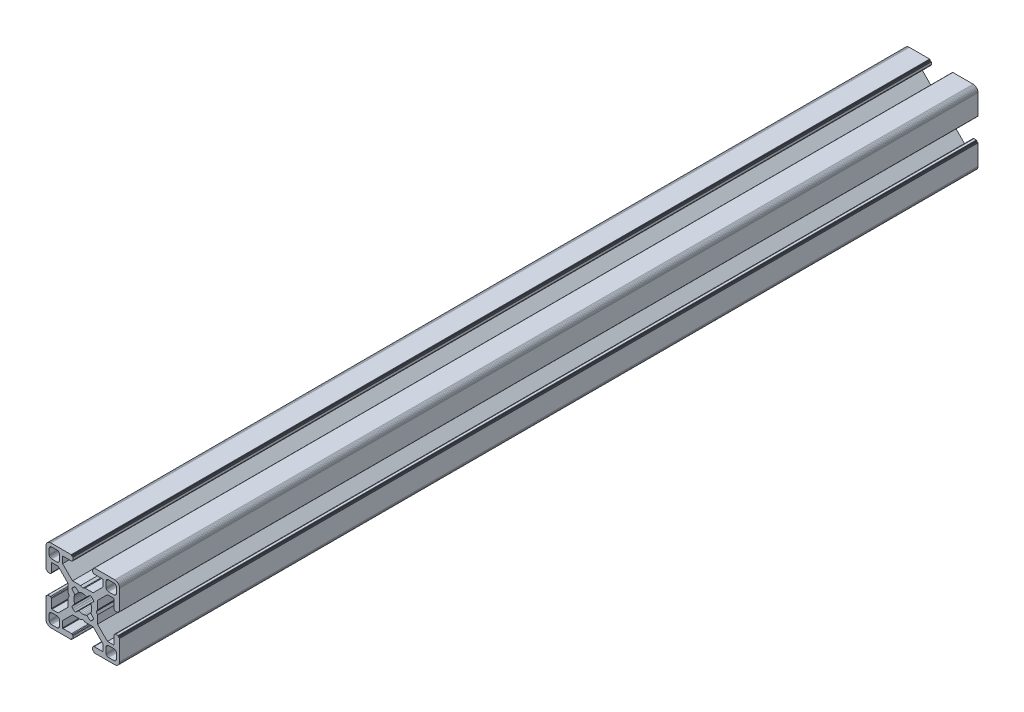
SolidWorks part; units mm, degrees
ref_plane "Front Plane" through (0, 0, 0) normal (0, 0, 1) x (1, 0, 0)
ref_plane "Top Plane" through (0, 0, 0) normal (0, 1, 0) x (1, 0, 0)
ref_plane "Right Plane" through (0, 0, 0) normal (1, 0, 0) x (0, 0, -1)
ref_plane "Plane1" through (0, 0, 0) normal (0, 0, 1) x (1, 0, 0)
sketch "Sketch1" plane through (0, 0, 0) normal (0, 0, 1) x (1, 0, 0)
  line L0 (28.3473, 29.9696) -> (28, 30)
  line L1 (28, 30) -> (19.75, 30)
  line L2 (19.75, 30) -> (19.7153, 29.997)
  line L3 (19.7153, 29.997) -> (19.6816, 29.9879)
  line L4 (19.6816, 29.9879) -> (19.65, 29.9732)
  line L5 (19.65, 29.9732) -> (19.6214, 29.9532)
  line L6 (19.6214, 29.9532) -> (19.5968, 29.9286)
  line L7 (19.5968, 29.9286) -> (19.5768, 29.9)
  line L8 (19.5768, 29.9) -> (19.5621, 29.8684)
  line L9 (19.5621, 29.8684) -> (19.553, 29.8347)
  line L10 (19.553, 29.8347) -> (19.55, 29.8)
  line L11 (19.55, 29.8) -> (19.55, 29.7)
  line L12 (19.55, 29.7) -> (19.547, 29.6653)
  line L13 (19.547, 29.6653) -> (19.5379, 29.6316)
  line L14 (19.5379, 29.6316) -> (19.5232, 29.6)
  line L15 (19.5232, 29.6) -> (19.5032, 29.5714)
  line L16 (19.5032, 29.5714) -> (19.4786, 29.5468)
  line L17 (19.4786, 29.5468) -> (19.45, 29.5268)
  line L18 (19.45, 29.5268) -> (19.4184, 29.5121)
  line L19 (19.4184, 29.5121) -> (19.3847, 29.503)
  line L20 (19.3847, 29.503) -> (19.35, 29.5)
  line L21 (19.35, 29.5) -> (19.25, 29.5)
  line L22 (19.25, 29.5) -> (19.2153, 29.497)
  line L23 (19.2153, 29.497) -> (19.1816, 29.4879)
  line L24 (19.1816, 29.4879) -> (19.15, 29.4732)
  line L25 (19.15, 29.4732) -> (19.1214, 29.4532)
  line L26 (19.1214, 29.4532) -> (19.0968, 29.4286)
  line L27 (19.0968, 29.4286) -> (19.0768, 29.4)
  line L28 (19.0768, 29.4) -> (19.0621, 29.3684)
  line L29 (19.0621, 29.3684) -> (19.053, 29.3347)
  line L30 (19.053, 29.3347) -> (19.05, 29.3)
  line L31 (19.05, 29.3) -> (19.05, 28.4)
  line L32 (19.05, 28.4) -> (19.0591, 28.2958)
  line L33 (19.0591, 28.2958) -> (19.0862, 28.1948)
  line L34 (19.0862, 28.1948) -> (19.1304, 28.1)
  line L35 (19.1304, 28.1) -> (19.1904, 28.0143)
  line L36 (19.1904, 28.0143) -> (19.2643, 27.9404)
  line L37 (19.2643, 27.9404) -> (19.35, 27.8804)
  line L38 (19.35, 27.8804) -> (19.4448, 27.8362)
  line L39 (19.4448, 27.8362) -> (19.5458, 27.8091)
  line L40 (19.5458, 27.8091) -> (19.65, 27.8)
  line L41 (19.65, 27.8) -> (23.05, 27.8)
  line L42 (23.05, 27.8) -> (23.0847, 27.7969)
  line L43 (23.0847, 27.7969) -> (23.1184, 27.7879)
  line L44 (23.1184, 27.7879) -> (23.15, 27.7732)
  line L45 (23.15, 27.7732) -> (23.1786, 27.7532)
  line L46 (23.1786, 27.7532) -> (23.2032, 27.7285)
  line L47 (23.2032, 27.7285) -> (23.2232, 27.7)
  line L48 (23.2232, 27.7) -> (23.2379, 27.6684)
  line L49 (23.2379, 27.6684) -> (23.247, 27.6347)
  line L50 (23.247, 27.6347) -> (23.25, 27.6)
  line L51 (23.25, 27.6) -> (23.25, 25.05)
  line L52 (23.25, 25.05) -> (19.2045, 21)
  line L53 (19.2045, 21) -> (15.9, 21)
  line L54 (15.9, 21) -> (15, 20.4848)
  line L55 (15, 20.4848) -> (14.1, 21)
  line L56 (14.1, 21) -> (10.7955, 21)
  line L57 (10.7955, 21) -> (7.9973, 23.8013)
  line L58 (7.9973, 23.8013) -> (6.75, 25.05)
  line L59 (6.75, 25.05) -> (6.75, 27.6)
  line L60 (6.75, 27.6) -> (6.753, 27.6347)
  line L61 (6.753, 27.6347) -> (6.7621, 27.6684)
  line L62 (6.7621, 27.6684) -> (6.7768, 27.7)
  line L63 (6.7768, 27.7) -> (6.7968, 27.7285)
  line L64 (6.7968, 27.7285) -> (6.8215, 27.7532)
  line L65 (6.8215, 27.7532) -> (6.85, 27.7732)
  line L66 (6.85, 27.7732) -> (6.8816, 27.7879)
  line L67 (6.8816, 27.7879) -> (6.9153, 27.7969)
  line L68 (6.9153, 27.7969) -> (6.95, 27.8)
  line L69 (6.95, 27.8) -> (10.35, 27.8)
  line L70 (10.35, 27.8) -> (10.4542, 27.8091)
  line L71 (10.4542, 27.8091) -> (10.5552, 27.8362)
  line L72 (10.5552, 27.8362) -> (10.65, 27.8804)
  line L73 (10.65, 27.8804) -> (10.7357, 27.9404)
  line L74 (10.7357, 27.9404) -> (10.8096, 28.0143)
  line L75 (10.8096, 28.0143) -> (10.8696, 28.1)
  line L76 (10.8696, 28.1) -> (10.9138, 28.1948)
  line L77 (10.9138, 28.1948) -> (10.9409, 28.2958)
  line L78 (10.9409, 28.2958) -> (10.95, 28.4)
  line L79 (10.95, 28.4) -> (10.95, 29.3)
  line L80 (10.95, 29.3) -> (10.947, 29.3347)
  line L81 (10.947, 29.3347) -> (10.938, 29.3684)
  line L82 (10.938, 29.3684) -> (10.9232, 29.4)
  line L83 (10.9232, 29.4) -> (10.9032, 29.4286)
  line L84 (10.9032, 29.4286) -> (10.8786, 29.4532)
  line L85 (10.8786, 29.4532) -> (10.85, 29.4732)
  line L86 (10.85, 29.4732) -> (10.8184, 29.4879)
  line L87 (10.8184, 29.4879) -> (10.7847, 29.497)
  line L88 (10.7847, 29.497) -> (10.75, 29.5)
  line L89 (10.75, 29.5) -> (10.65, 29.5)
  line L90 (10.65, 29.5) -> (10.6153, 29.503)
  line L91 (10.6153, 29.503) -> (10.5816, 29.5121)
  line L92 (10.5816, 29.5121) -> (10.55, 29.5268)
  line L93 (10.55, 29.5268) -> (10.5214, 29.5468)
  line L94 (10.5214, 29.5468) -> (10.4968, 29.5714)
  line L95 (10.4968, 29.5714) -> (10.4768, 29.6)
  line L96 (10.4768, 29.6) -> (10.4621, 29.6316)
  line L97 (10.4621, 29.6316) -> (10.453, 29.6653)
  line L98 (10.453, 29.6653) -> (10.45, 29.7)
  line L99 (10.45, 29.7) -> (10.45, 29.8)
  line L100 (10.45, 29.8) -> (10.447, 29.8347)
  line L101 (10.447, 29.8347) -> (10.4379, 29.8684)
  line L102 (10.4379, 29.8684) -> (10.4232, 29.9)
  line L103 (10.4232, 29.9) -> (10.4032, 29.9286)
  line L104 (10.4032, 29.9286) -> (10.3786, 29.9532)
  line L105 (10.3786, 29.9532) -> (10.35, 29.9732)
  line L106 (10.35, 29.9732) -> (10.3184, 29.9879)
  line L107 (10.3184, 29.9879) -> (10.2847, 29.997)
  line L108 (10.2847, 29.997) -> (10.25, 30)
  line L109 (10.25, 30) -> (2, 30)
  line L110 (2, 30) -> (1.6527, 29.9696)
  line L111 (1.6527, 29.9696) -> (1.316, 29.8794)
  line L112 (1.316, 29.8794) -> (1, 29.7321)
  line L113 (1, 29.7321) -> (0.7144, 29.5321)
  line L114 (0.7144, 29.5321) -> (0.4679, 29.2856)
  line L115 (0.4679, 29.2856) -> (0.2679, 29)
  line L116 (0.2679, 29) -> (0.1206, 28.684)
  line L117 (0.1206, 28.684) -> (0.0304, 28.3473)
  line L118 (0.0304, 28.3473) -> (0, 28)
  line L119 (0, 28) -> (0, 19.75)
  line L120 (0, 19.75) -> (0.003, 19.7153)
  line L121 (0.003, 19.7153) -> (0.0121, 19.6816)
  line L122 (0.0121, 19.6816) -> (0.0268, 19.65)
  line L123 (0.0268, 19.65) -> (0.0468, 19.6214)
  line L124 (0.0468, 19.6214) -> (0.0714, 19.5968)
  line L125 (0.0714, 19.5968) -> (0.1, 19.5768)
  line L126 (0.1, 19.5768) -> (0.1316, 19.5621)
  line L127 (0.1316, 19.5621) -> (0.1653, 19.553)
  line L128 (0.1653, 19.553) -> (0.2, 19.55)
  line L129 (0.2, 19.55) -> (0.3, 19.55)
  line L130 (0.3, 19.55) -> (0.3347, 19.547)
  line L131 (0.3347, 19.547) -> (0.3684, 19.5379)
  line L132 (0.3684, 19.5379) -> (0.4, 19.5232)
  line L133 (0.4, 19.5232) -> (0.4286, 19.5032)
  line L134 (0.4286, 19.5032) -> (0.4532, 19.4786)
  line L135 (0.4532, 19.4786) -> (0.4732, 19.45)
  line L136 (0.4732, 19.45) -> (0.4879, 19.4184)
  line L137 (0.4879, 19.4184) -> (0.497, 19.3847)
  line L138 (0.497, 19.3847) -> (0.5, 19.35)
  line L139 (0.5, 19.35) -> (0.5, 19.25)
  line L140 (0.5, 19.25) -> (0.503, 19.2153)
  line L141 (0.503, 19.2153) -> (0.5121, 19.1816)
  line L142 (0.5121, 19.1816) -> (0.5268, 19.15)
  line L143 (0.5268, 19.15) -> (0.5468, 19.1214)
  line L144 (0.5468, 19.1214) -> (0.5714, 19.0968)
  line L145 (0.5714, 19.0968) -> (0.6, 19.0768)
  line L146 (0.6, 19.0768) -> (0.6316, 19.0621)
  line L147 (0.6316, 19.0621) -> (0.6653, 19.053)
  line L148 (0.6653, 19.053) -> (0.7, 19.05)
  line L149 (0.7, 19.05) -> (1.6, 19.05)
  line L150 (1.6, 19.05) -> (1.7042, 19.0591)
  line L151 (1.7042, 19.0591) -> (1.8052, 19.0862)
  line L152 (1.8052, 19.0862) -> (1.9, 19.1304)
  line L153 (1.9, 19.1304) -> (1.9857, 19.1904)
  line L154 (1.9857, 19.1904) -> (2.0596, 19.2643)
  line L155 (2.0596, 19.2643) -> (2.1196, 19.35)
  line L156 (2.1196, 19.35) -> (2.1638, 19.4448)
  line L157 (2.1638, 19.4448) -> (2.1909, 19.5458)
  line L158 (2.1909, 19.5458) -> (2.2, 19.65)
  line L159 (2.2, 19.65) -> (2.2, 23.05)
  line L160 (2.2, 23.05) -> (2.203, 23.0847)
  line L161 (2.203, 23.0847) -> (2.2121, 23.1184)
  line L162 (2.2121, 23.1184) -> (2.2268, 23.15)
  line L163 (2.2268, 23.15) -> (2.2468, 23.1786)
  line L164 (2.2468, 23.1786) -> (2.2714, 23.2032)
  line L165 (2.2714, 23.2032) -> (2.3, 23.2232)
  line L166 (2.3, 23.2232) -> (2.3316, 23.2379)
  line L167 (2.3316, 23.2379) -> (2.3653, 23.247)
  line L168 (2.3653, 23.247) -> (2.4, 23.25)
  line L169 (2.4, 23.25) -> (4.95, 23.25)
  line L170 (4.95, 23.25) -> (7.9973, 20.2027)
  line L171 (7.9973, 20.2027) -> (8.9955, 19.2045)
  line L172 (8.9955, 19.2045) -> (8.9955, 15.9)
  line L173 (8.9955, 15.9) -> (9.5151, 15)
  line L174 (9.5151, 15) -> (8.9955, 14.1)
  line L175 (8.9955, 14.1) -> (8.9955, 10.7955)
  line L176 (8.9955, 10.7955) -> (4.95, 6.75)
  line L177 (4.95, 6.75) -> (2.4, 6.75)
  line L178 (2.4, 6.75) -> (2.3653, 6.753)
  line L179 (2.3653, 6.753) -> (2.3316, 6.7621)
  line L180 (2.3316, 6.7621) -> (2.3, 6.7768)
  line L181 (2.3, 6.7768) -> (2.2714, 6.7968)
  line L182 (2.2714, 6.7968) -> (2.2468, 6.8214)
  line L183 (2.2468, 6.8214) -> (2.2268, 6.85)
  line L184 (2.2268, 6.85) -> (2.2121, 6.8816)
  line L185 (2.2121, 6.8816) -> (2.203, 6.9153)
  line L186 (2.203, 6.9153) -> (2.2, 6.95)
  line L187 (2.2, 6.95) -> (2.2, 10.35)
  line L188 (2.2, 10.35) -> (2.1909, 10.4542)
  line L189 (2.1909, 10.4542) -> (2.1638, 10.5552)
  line L190 (2.1638, 10.5552) -> (2.1196, 10.65)
  line L191 (2.1196, 10.65) -> (2.0596, 10.7357)
  line L192 (2.0596, 10.7357) -> (1.9857, 10.8096)
  line L193 (1.9857, 10.8096) -> (1.9, 10.8696)
  line L194 (1.9, 10.8696) -> (1.8052, 10.9138)
  line L195 (1.8052, 10.9138) -> (1.7042, 10.9409)
  line L196 (1.7042, 10.9409) -> (1.6, 10.95)
  line L197 (1.6, 10.95) -> (0.7, 10.95)
  line L198 (0.7, 10.95) -> (0.6653, 10.9469)
  line L199 (0.6653, 10.9469) -> (0.6316, 10.9379)
  line L200 (0.6316, 10.9379) -> (0.6, 10.9232)
  line L201 (0.6, 10.9232) -> (0.5715, 10.9032)
  line L202 (0.5715, 10.9032) -> (0.5468, 10.8785)
  line L203 (0.5468, 10.8785) -> (0.5268, 10.85)
  line L204 (0.5268, 10.85) -> (0.5121, 10.8184)
  line L205 (0.5121, 10.8184) -> (0.503, 10.7847)
  line L206 (0.503, 10.7847) -> (0.5, 10.75)
  line L207 (0.5, 10.75) -> (0.5, 10.65)
  line L208 (0.5, 10.65) -> (0.497, 10.6153)
  line L209 (0.497, 10.6153) -> (0.4879, 10.5816)
  line L210 (0.4879, 10.5816) -> (0.4732, 10.55)
  line L211 (0.4732, 10.55) -> (0.4532, 10.5214)
  line L212 (0.4532, 10.5214) -> (0.4286, 10.4968)
  line L213 (0.4286, 10.4968) -> (0.4, 10.4768)
  line L214 (0.4, 10.4768) -> (0.3684, 10.4621)
  line L215 (0.3684, 10.4621) -> (0.3347, 10.453)
  line L216 (0.3347, 10.453) -> (0.3, 10.45)
  line L217 (0.3, 10.45) -> (0.2, 10.45)
  line L218 (0.2, 10.45) -> (0.1653, 10.447)
  line L219 (0.1653, 10.447) -> (0.1316, 10.4379)
  line L220 (0.1316, 10.4379) -> (0.1, 10.4232)
  line L221 (0.1, 10.4232) -> (0.0714, 10.4032)
  line L222 (0.0714, 10.4032) -> (0.0468, 10.3786)
  line L223 (0.0468, 10.3786) -> (0.0268, 10.35)
  line L224 (0.0268, 10.35) -> (0.0121, 10.3184)
  line L225 (0.0121, 10.3184) -> (0.003, 10.2847)
  line L226 (0.003, 10.2847) -> (0, 10.25)
  line L227 (0, 10.25) -> (0, 2)
  line L228 (0, 2) -> (0.0304, 1.6527)
  line L229 (0.0304, 1.6527) -> (0.1206, 1.316)
  line L230 (0.1206, 1.316) -> (0.2679, 1)
  line L231 (0.2679, 1) -> (0.4679, 0.7144)
  line L232 (0.4679, 0.7144) -> (0.7144, 0.4679)
  line L233 (0.7144, 0.4679) -> (1, 0.2679)
  line L234 (1, 0.2679) -> (1.316, 0.1206)
  line L235 (1.316, 0.1206) -> (1.6527, 0.0304)
  line L236 (1.6527, 0.0304) -> (2, 0)
  line L237 (2, 0) -> (10.25, 0)
  line L238 (10.25, 0) -> (10.2847, 0.003)
  line L239 (10.2847, 0.003) -> (10.3184, 0.0121)
  line L240 (10.3184, 0.0121) -> (10.35, 0.0268)
  line L241 (10.35, 0.0268) -> (10.3786, 0.0468)
  line L242 (10.3786, 0.0468) -> (10.4032, 0.0714)
  line L243 (10.4032, 0.0714) -> (10.4232, 0.1)
  line L244 (10.4232, 0.1) -> (10.4379, 0.1316)
  line L245 (10.4379, 0.1316) -> (10.447, 0.1653)
  line L246 (10.447, 0.1653) -> (10.45, 0.2)
  line L247 (10.45, 0.2) -> (10.45, 0.3)
  line L248 (10.45, 0.3) -> (10.453, 0.3347)
  line L249 (10.453, 0.3347) -> (10.4621, 0.3684)
  line L250 (10.4621, 0.3684) -> (10.4768, 0.4)
  line L251 (10.4768, 0.4) -> (10.4968, 0.4286)
  line L252 (10.4968, 0.4286) -> (10.5214, 0.4532)
  line L253 (10.5214, 0.4532) -> (10.55, 0.4732)
  line L254 (10.55, 0.4732) -> (10.5816, 0.4879)
  line L255 (10.5816, 0.4879) -> (10.6153, 0.497)
  line L256 (10.6153, 0.497) -> (10.65, 0.5)
  line L257 (10.65, 0.5) -> (10.75, 0.5)
  line L258 (10.75, 0.5) -> (10.7847, 0.503)
  line L259 (10.7847, 0.503) -> (10.8184, 0.5121)
  line L260 (10.8184, 0.5121) -> (10.85, 0.5268)
  line L261 (10.85, 0.5268) -> (10.8785, 0.5468)
  line L262 (10.8785, 0.5468) -> (10.9032, 0.5715)
  line L263 (10.9032, 0.5715) -> (10.9232, 0.6)
  line L264 (10.9232, 0.6) -> (10.9379, 0.6316)
  line L265 (10.9379, 0.6316) -> (10.9469, 0.6653)
  line L266 (10.9469, 0.6653) -> (10.95, 0.7)
  line L267 (10.95, 0.7) -> (10.95, 1.6)
  line L268 (10.95, 1.6) -> (10.9409, 1.7042)
  line L269 (10.9409, 1.7042) -> (10.9138, 1.8052)
  line L270 (10.9138, 1.8052) -> (10.8696, 1.9)
  line L271 (10.8696, 1.9) -> (10.8096, 1.9857)
  line L272 (10.8096, 1.9857) -> (10.7357, 2.0596)
  line L273 (10.7357, 2.0596) -> (10.65, 2.1196)
  line L274 (10.65, 2.1196) -> (10.5552, 2.1638)
  line L275 (10.5552, 2.1638) -> (10.4542, 2.1909)
  line L276 (10.4542, 2.1909) -> (10.35, 2.2)
  line L277 (10.35, 2.2) -> (6.95, 2.2)
  line L278 (6.95, 2.2) -> (6.9153, 2.203)
  line L279 (6.9153, 2.203) -> (6.8816, 2.212)
  line L280 (6.8816, 2.212) -> (6.85, 2.2268)
  line L281 (6.85, 2.2268) -> (6.8215, 2.2468)
  line L282 (6.8215, 2.2468) -> (6.7968, 2.2714)
  line L283 (6.7968, 2.2714) -> (6.7768, 2.3)
  line L284 (6.7768, 2.3) -> (6.7621, 2.3316)
  line L285 (6.7621, 2.3316) -> (6.753, 2.3653)
  line L286 (6.753, 2.3653) -> (6.75, 2.4)
  line L287 (6.75, 2.4) -> (6.75, 4.95)
  line L288 (6.75, 4.95) -> (9.7875, 7.9908)
  line L289 (9.7875, 7.9908) -> (10.7955, 9)
  line L290 (10.7955, 9) -> (14.1, 9)
  line L291 (14.1, 9) -> (15, 9.5151)
  line L292 (15, 9.5151) -> (15.9, 9)
  line L293 (15.9, 9) -> (19.2045, 9)
  line L294 (19.2045, 9) -> (20.2126, 7.9908)
  line L295 (20.2126, 7.9908) -> (23.25, 4.95)
  line L296 (23.25, 4.95) -> (23.25, 2.4)
  line L297 (23.25, 2.4) -> (23.247, 2.3653)
  line L298 (23.247, 2.3653) -> (23.2379, 2.3316)
  line L299 (23.2379, 2.3316) -> (23.2232, 2.3)
  line L300 (23.2232, 2.3) -> (23.2032, 2.2714)
  line L301 (23.2032, 2.2714) -> (23.1786, 2.2468)
  line L302 (23.1786, 2.2468) -> (23.15, 2.2268)
  line L303 (23.15, 2.2268) -> (23.1184, 2.212)
  line L304 (23.1184, 2.212) -> (23.0847, 2.203)
  line L305 (23.0847, 2.203) -> (23.05, 2.2)
  line L306 (23.05, 2.2) -> (19.65, 2.2)
  line L307 (19.65, 2.2) -> (19.5458, 2.1909)
  line L308 (19.5458, 2.1909) -> (19.4448, 2.1638)
  line L309 (19.4448, 2.1638) -> (19.35, 2.1196)
  line L310 (19.35, 2.1196) -> (19.2643, 2.0596)
  line L311 (19.2643, 2.0596) -> (19.1904, 1.9857)
  line L312 (19.1904, 1.9857) -> (19.1304, 1.9)
  line L313 (19.1304, 1.9) -> (19.0862, 1.8052)
  line L314 (19.0862, 1.8052) -> (19.0591, 1.7042)
  line L315 (19.0591, 1.7042) -> (19.05, 1.6)
  line L316 (19.05, 1.6) -> (19.05, 0.7)
  line L317 (19.05, 0.7) -> (19.053, 0.6653)
  line L318 (19.053, 0.6653) -> (19.0621, 0.6316)
  line L319 (19.0621, 0.6316) -> (19.0768, 0.6)
  line L320 (19.0768, 0.6) -> (19.0968, 0.5714)
  line L321 (19.0968, 0.5714) -> (19.1214, 0.5468)
  line L322 (19.1214, 0.5468) -> (19.15, 0.5268)
  line L323 (19.15, 0.5268) -> (19.1816, 0.5121)
  line L324 (19.1816, 0.5121) -> (19.2153, 0.503)
  line L325 (19.2153, 0.503) -> (19.25, 0.5)
  line L326 (19.25, 0.5) -> (19.35, 0.5)
  line L327 (19.35, 0.5) -> (19.3847, 0.497)
  line L328 (19.3847, 0.497) -> (19.4184, 0.4879)
  line L329 (19.4184, 0.4879) -> (19.45, 0.4732)
  line L330 (19.45, 0.4732) -> (19.4786, 0.4532)
  line L331 (19.4786, 0.4532) -> (19.5032, 0.4286)
  line L332 (19.5032, 0.4286) -> (19.5232, 0.4)
  line L333 (19.5232, 0.4) -> (19.5379, 0.3684)
  line L334 (19.5379, 0.3684) -> (19.547, 0.3347)
  line L335 (19.547, 0.3347) -> (19.55, 0.3)
  line L336 (19.55, 0.3) -> (19.55, 0.2)
  line L337 (19.55, 0.2) -> (19.553, 0.1653)
  line L338 (19.553, 0.1653) -> (19.5621, 0.1316)
  line L339 (19.5621, 0.1316) -> (19.5768, 0.1)
  line L340 (19.5768, 0.1) -> (19.5968, 0.0714)
  line L341 (19.5968, 0.0714) -> (19.6214, 0.0468)
  line L342 (19.6214, 0.0468) -> (19.65, 0.0268)
  line L343 (19.65, 0.0268) -> (19.6816, 0.0121)
  line L344 (19.6816, 0.0121) -> (19.7153, 0.003)
  line L345 (19.7153, 0.003) -> (19.75, 0)
  line L346 (19.75, 0) -> (28, 0)
  line L347 (28, 0) -> (28.3473, 0.0304)
  line L348 (28.3473, 0.0304) -> (28.684, 0.1206)
  line L349 (28.684, 0.1206) -> (29, 0.2679)
  line L350 (29, 0.2679) -> (29.2856, 0.4679)
  line L351 (29.2856, 0.4679) -> (29.5321, 0.7144)
  line L352 (29.5321, 0.7144) -> (29.7321, 1)
  line L353 (29.7321, 1) -> (29.8794, 1.316)
  line L354 (29.8794, 1.316) -> (29.9696, 1.6527)
  line L355 (29.9696, 1.6527) -> (30, 2)
  line L356 (30, 2) -> (30, 10.25)
  line L357 (30, 10.25) -> (29.997, 10.2847)
  line L358 (29.997, 10.2847) -> (29.988, 10.3184)
  line L359 (29.988, 10.3184) -> (29.9732, 10.35)
  line L360 (29.9732, 10.35) -> (29.9532, 10.3785)
  line L361 (29.9532, 10.3785) -> (29.9286, 10.4032)
  line L362 (29.9286, 10.4032) -> (29.9, 10.4232)
  line L363 (29.9, 10.4232) -> (29.8684, 10.4379)
  line L364 (29.8684, 10.4379) -> (29.8347, 10.447)
  line L365 (29.8347, 10.447) -> (29.8, 10.45)
  line L366 (29.8, 10.45) -> (29.7, 10.45)
  line L367 (29.7, 10.45) -> (29.6649, 10.4534)
  line L368 (29.6649, 10.4534) -> (29.6312, 10.4624)
  line L369 (29.6312, 10.4624) -> (29.5996, 10.4772)
  line L370 (29.5996, 10.4772) -> (29.5711, 10.4972)
  line L371 (29.5711, 10.4972) -> (29.5464, 10.5218)
  line L372 (29.5464, 10.5218) -> (29.5264, 10.5504)
  line L373 (29.5264, 10.5504) -> (29.5117, 10.582)
  line L374 (29.5117, 10.582) -> (29.5027, 10.6156)
  line L375 (29.5027, 10.6156) -> (29.4996, 10.6504)
  line L376 (29.4996, 10.6504) -> (29.4996, 10.7504)
  line L377 (29.4996, 10.7504) -> (29.497, 10.7847)
  line L378 (29.497, 10.7847) -> (29.4879, 10.8184)
  line L379 (29.4879, 10.8184) -> (29.4732, 10.85)
  line L380 (29.4732, 10.85) -> (29.4532, 10.8785)
  line L381 (29.4532, 10.8785) -> (29.4286, 10.9032)
  line L382 (29.4286, 10.9032) -> (29.4, 10.9232)
  line L383 (29.4, 10.9232) -> (29.3684, 10.9379)
  line L384 (29.3684, 10.9379) -> (29.3347, 10.9469)
  line L385 (29.3347, 10.9469) -> (29.3, 10.95)
  line L386 (29.3, 10.95) -> (28.4, 10.95)
  line L387 (28.4, 10.95) -> (28.2958, 10.9409)
  line L388 (28.2958, 10.9409) -> (28.1948, 10.9138)
  line L389 (28.1948, 10.9138) -> (28.1, 10.8696)
  line L390 (28.1, 10.8696) -> (28.0143, 10.8096)
  line L391 (28.0143, 10.8096) -> (27.9404, 10.7357)
  line L392 (27.9404, 10.7357) -> (27.8804, 10.65)
  line L393 (27.8804, 10.65) -> (27.8362, 10.5552)
  line L394 (27.8362, 10.5552) -> (27.8091, 10.4542)
  line L395 (27.8091, 10.4542) -> (27.8, 10.35)
  line L396 (27.8, 10.35) -> (27.8, 6.95)
  line L397 (27.8, 6.95) -> (27.797, 6.9153)
  line L398 (27.797, 6.9153) -> (27.7879, 6.8816)
  line L399 (27.7879, 6.8816) -> (27.7732, 6.85)
  line L400 (27.7732, 6.85) -> (27.7532, 6.8214)
  line L401 (27.7532, 6.8214) -> (27.7286, 6.7968)
  line L402 (27.7286, 6.7968) -> (27.7, 6.7768)
  line L403 (27.7, 6.7768) -> (27.6684, 6.7621)
  line L404 (27.6684, 6.7621) -> (27.6347, 6.753)
  line L405 (27.6347, 6.753) -> (27.6, 6.75)
  line L406 (27.6, 6.75) -> (25.05, 6.75)
  line L407 (25.05, 6.75) -> (23.8092, 7.9908)
  line L408 (23.8092, 7.9908) -> (21.0045, 10.7955)
  line L409 (21.0045, 10.7955) -> (21.0045, 14.1)
  line L410 (21.0045, 14.1) -> (20.4849, 15)
  line L411 (20.4849, 15) -> (21.0045, 15.9)
  line L412 (21.0045, 15.9) -> (21.0045, 19.2045)
  line L413 (21.0045, 19.2045) -> (25.05, 23.25)
  line L414 (25.05, 23.25) -> (27.6, 23.25)
  line L415 (27.6, 23.25) -> (27.6347, 23.247)
  line L416 (27.6347, 23.247) -> (27.6684, 23.2379)
  line L417 (27.6684, 23.2379) -> (27.7, 23.2232)
  line L418 (27.7, 23.2232) -> (27.7286, 23.2032)
  line L419 (27.7286, 23.2032) -> (27.7532, 23.1786)
  line L420 (27.7532, 23.1786) -> (27.7732, 23.15)
  line L421 (27.7732, 23.15) -> (27.7879, 23.1184)
  line L422 (27.7879, 23.1184) -> (27.797, 23.0847)
  line L423 (27.797, 23.0847) -> (27.8, 23.05)
  line L424 (27.8, 23.05) -> (27.8, 19.65)
  line L425 (27.8, 19.65) -> (27.8091, 19.5458)
  line L426 (27.8091, 19.5458) -> (27.8362, 19.4448)
  line L427 (27.8362, 19.4448) -> (27.8804, 19.35)
  line L428 (27.8804, 19.35) -> (27.9404, 19.2643)
  line L429 (27.9404, 19.2643) -> (28.0143, 19.1904)
  line L430 (28.0143, 19.1904) -> (28.1, 19.1304)
  line L431 (28.1, 19.1304) -> (28.1948, 19.0862)
  line L432 (28.1948, 19.0862) -> (28.2958, 19.0591)
  line L433 (28.2958, 19.0591) -> (28.4, 19.05)
  line L434 (28.4, 19.05) -> (29.3, 19.05)
  line L435 (29.3, 19.05) -> (29.3347, 19.053)
  line L436 (29.3347, 19.053) -> (29.3684, 19.0621)
  line L437 (29.3684, 19.0621) -> (29.4, 19.0768)
  line L438 (29.4, 19.0768) -> (29.4282, 19.0971)
  line L439 (29.4282, 19.0971) -> (29.4528, 19.1218)
  line L440 (29.4528, 19.1218) -> (29.4728, 19.1504)
  line L441 (29.4728, 19.1504) -> (29.4876, 19.182)
  line L442 (29.4876, 19.182) -> (29.4966, 19.2156)
  line L443 (29.4966, 19.2156) -> (29.4996, 19.2504)
  line L444 (29.4996, 19.2504) -> (29.4996, 19.3504)
  line L445 (29.4996, 19.3504) -> (29.5027, 19.3851)
  line L446 (29.5027, 19.3851) -> (29.5117, 19.4188)
  line L447 (29.5117, 19.4188) -> (29.5264, 19.4504)
  line L448 (29.5264, 19.4504) -> (29.5464, 19.4789)
  line L449 (29.5464, 19.4789) -> (29.5711, 19.5036)
  line L450 (29.5711, 19.5036) -> (29.5996, 19.5236)
  line L451 (29.5996, 19.5236) -> (29.6312, 19.5383)
  line L452 (29.6312, 19.5383) -> (29.6649, 19.5473)
  line L453 (29.6649, 19.5473) -> (29.7, 19.55)
  line L454 (29.7, 19.55) -> (29.8, 19.55)
  line L455 (29.8, 19.55) -> (29.8347, 19.553)
  line L456 (29.8347, 19.553) -> (29.8684, 19.5621)
  line L457 (29.8684, 19.5621) -> (29.9, 19.5768)
  line L458 (29.9, 19.5768) -> (29.9286, 19.5968)
  line L459 (29.9286, 19.5968) -> (29.9532, 19.6214)
  line L460 (29.9532, 19.6214) -> (29.9732, 19.65)
  line L461 (29.9732, 19.65) -> (29.9879, 19.6816)
  line L462 (29.9879, 19.6816) -> (29.997, 19.7153)
  line L463 (29.997, 19.7153) -> (30, 19.75)
  line L464 (30, 19.75) -> (30, 28)
  line L465 (30, 28) -> (29.9696, 28.3473)
  line L466 (29.9696, 28.3473) -> (29.8794, 28.684)
  line L467 (29.8794, 28.684) -> (29.7321, 29)
  line L468 (29.7321, 29) -> (29.5321, 29.2856)
  line L469 (29.5321, 29.2856) -> (29.2856, 29.5321)
  line L470 (29.2856, 29.5321) -> (29, 29.7321)
  line L471 (29, 29.7321) -> (28.684, 29.8794)
  line L472 (28.684, 29.8794) -> (28.3473, 29.9696)
  line L473 (1.3, 25.5) -> (1.3, 27.7)
  line L474 (1.3, 27.7) -> (1.3123, 27.8564)
  line L475 (1.3123, 27.8564) -> (1.3489, 28.009)
  line L476 (1.3489, 28.009) -> (1.409, 28.154)
  line L477 (1.409, 28.154) -> (1.491, 28.2878)
  line L478 (1.491, 28.2878) -> (1.5929, 28.4071)
  line L479 (1.5929, 28.4071) -> (1.7122, 28.509)
  line L480 (1.7122, 28.509) -> (1.846, 28.591)
  line L481 (1.846, 28.591) -> (1.991, 28.6511)
  line L482 (1.991, 28.6511) -> (2.1436, 28.6877)
  line L483 (2.1436, 28.6877) -> (2.3, 28.7)
  line L484 (2.3, 28.7) -> (4.5, 28.7)
  line L485 (4.5, 28.7) -> (4.6564, 28.6877)
  line L486 (4.6564, 28.6877) -> (4.809, 28.6511)
  line L487 (4.809, 28.6511) -> (4.954, 28.591)
  line L488 (4.954, 28.591) -> (5.0878, 28.509)
  line L489 (5.0878, 28.509) -> (5.2071, 28.4071)
  line L490 (5.2071, 28.4071) -> (5.309, 28.2878)
  line L491 (5.309, 28.2878) -> (5.391, 28.154)
  line L492 (5.391, 28.154) -> (5.4511, 28.009)
  line L493 (5.4511, 28.009) -> (5.4877, 27.8564)
  line L494 (5.4877, 27.8564) -> (5.5, 27.7)
  line L495 (5.5, 27.7) -> (5.5, 25.5)
  line L496 (5.5, 25.5) -> (5.4877, 25.3436)
  line L497 (5.4877, 25.3436) -> (5.4511, 25.191)
  line L498 (5.4511, 25.191) -> (5.391, 25.046)
  line L499 (5.391, 25.046) -> (5.309, 24.9122)
  line L500 (5.309, 24.9122) -> (5.2071, 24.7929)
  line L501 (5.2071, 24.7929) -> (5.0878, 24.691)
  line L502 (5.0878, 24.691) -> (4.954, 24.609)
  line L503 (4.954, 24.609) -> (4.809, 24.5489)
  line L504 (4.809, 24.5489) -> (4.6564, 24.5123)
  line L505 (4.6564, 24.5123) -> (4.5, 24.5)
  line L506 (4.5, 24.5) -> (2.3, 24.5)
  line L507 (2.3, 24.5) -> (2.1436, 24.5123)
  line L508 (2.1436, 24.5123) -> (1.991, 24.5489)
  line L509 (1.991, 24.5489) -> (1.846, 24.609)
  line L510 (1.846, 24.609) -> (1.7122, 24.691)
  line L511 (1.7122, 24.691) -> (1.5929, 24.7929)
  line L512 (1.5929, 24.7929) -> (1.491, 24.9122)
  line L513 (1.491, 24.9122) -> (1.409, 25.046)
  line L514 (1.409, 25.046) -> (1.3489, 25.191)
  line L515 (1.3489, 25.191) -> (1.3123, 25.3436)
  line L516 (1.3123, 25.3436) -> (1.3, 25.5)
  line L517 (25.3436, 28.6877) -> (25.5, 28.7)
  line L518 (25.5, 28.7) -> (27.7, 28.7)
  line L519 (27.7, 28.7) -> (27.8564, 28.6877)
  line L520 (27.8564, 28.6877) -> (28.009, 28.6511)
  line L521 (28.009, 28.6511) -> (28.154, 28.591)
  line L522 (28.154, 28.591) -> (28.2878, 28.509)
  line L523 (28.2878, 28.509) -> (28.4071, 28.4071)
  line L524 (28.4071, 28.4071) -> (28.509, 28.2878)
  line L525 (28.509, 28.2878) -> (28.591, 28.154)
  line L526 (28.591, 28.154) -> (28.6511, 28.009)
  line L527 (28.6511, 28.009) -> (28.6877, 27.8564)
  line L528 (28.6877, 27.8564) -> (28.7, 27.7)
  line L529 (28.7, 27.7) -> (28.7, 25.5)
  line L530 (28.7, 25.5) -> (28.6877, 25.3436)
  line L531 (28.6877, 25.3436) -> (28.6511, 25.191)
  line L532 (28.6511, 25.191) -> (28.591, 25.046)
  line L533 (28.591, 25.046) -> (28.509, 24.9122)
  line L534 (28.509, 24.9122) -> (28.4071, 24.7929)
  line L535 (28.4071, 24.7929) -> (28.2878, 24.691)
  line L536 (28.2878, 24.691) -> (28.154, 24.609)
  line L537 (28.154, 24.609) -> (28.009, 24.5489)
  line L538 (28.009, 24.5489) -> (27.8564, 24.5123)
  line L539 (27.8564, 24.5123) -> (27.7, 24.5)
  line L540 (27.7, 24.5) -> (25.5, 24.5)
  line L541 (25.5, 24.5) -> (25.3436, 24.5123)
  line L542 (25.3436, 24.5123) -> (25.191, 24.5489)
  line L543 (25.191, 24.5489) -> (25.046, 24.609)
  line L544 (25.046, 24.609) -> (24.9122, 24.691)
  line L545 (24.9122, 24.691) -> (24.7929, 24.7929)
  line L546 (24.7929, 24.7929) -> (24.691, 24.9122)
  line L547 (24.691, 24.9122) -> (24.609, 25.046)
  line L548 (24.609, 25.046) -> (24.5489, 25.191)
  line L549 (24.5489, 25.191) -> (24.5123, 25.3436)
  line L550 (24.5123, 25.3436) -> (24.5, 25.5)
  line L551 (24.5, 25.5) -> (24.5, 27.7)
  line L552 (24.5, 27.7) -> (24.5123, 27.8564)
  line L553 (24.5123, 27.8564) -> (24.5489, 28.009)
  line L554 (24.5489, 28.009) -> (24.609, 28.154)
  line L555 (24.609, 28.154) -> (24.691, 28.2878)
  line L556 (24.691, 28.2878) -> (24.7929, 28.4071)
  line L557 (24.7929, 28.4071) -> (24.9122, 28.509)
  line L558 (24.9122, 28.509) -> (25.046, 28.591)
  line L559 (25.046, 28.591) -> (25.191, 28.6511)
  line L560 (25.191, 28.6511) -> (25.3436, 28.6877)
  line L561 (15, 18.65) -> (15.55, 18.6083)
  line L562 (15.55, 18.6083) -> (16.0875, 18.4842)
  line L563 (16.0875, 18.4842) -> (16.6001, 18.2806)
  line L564 (16.6001, 18.2806) -> (18.1359, 19.5184)
  line L565 (18.1359, 19.5184) -> (18.645, 19.1187)
  line L566 (18.645, 19.1187) -> (19.1036, 18.6621)
  line L567 (19.1036, 18.6621) -> (19.5053, 18.1547)
  line L568 (19.5053, 18.1547) -> (18.2806, 16.6001)
  line L569 (18.2806, 16.6001) -> (18.4842, 16.0875)
  line L570 (18.4842, 16.0875) -> (18.6083, 15.55)
  line L571 (18.6083, 15.55) -> (18.65, 15)
  line L572 (18.65, 15) -> (18.6083, 14.45)
  line L573 (18.6083, 14.45) -> (18.4842, 13.9125)
  line L574 (18.4842, 13.9125) -> (18.2806, 13.3999)
  line L575 (18.2806, 13.3999) -> (19.5053, 11.8453)
  line L576 (19.5053, 11.8453) -> (19.1036, 11.3379)
  line L577 (19.1036, 11.3379) -> (18.645, 10.8813)
  line L578 (18.645, 10.8813) -> (18.1359, 10.4816)
  line L579 (18.1359, 10.4816) -> (16.6001, 11.7194)
  line L580 (16.6001, 11.7194) -> (16.0875, 11.5158)
  line L581 (16.0875, 11.5158) -> (15.55, 11.3917)
  line L582 (15.55, 11.3917) -> (15, 11.35)
  line L583 (15, 11.35) -> (14.45, 11.3917)
  line L584 (14.45, 11.3917) -> (13.9125, 11.5158)
  line L585 (13.9125, 11.5158) -> (13.3999, 11.7194)
  line L586 (13.3999, 11.7194) -> (11.8641, 10.4816)
  line L587 (11.8641, 10.4816) -> (11.355, 10.8813)
  line L588 (11.355, 10.8813) -> (10.8964, 11.3379)
  line L589 (10.8964, 11.3379) -> (10.4947, 11.8453)
  line L590 (10.4947, 11.8453) -> (11.7194, 13.3999)
  line L591 (11.7194, 13.3999) -> (11.5158, 13.9125)
  line L592 (11.5158, 13.9125) -> (11.3917, 14.45)
  line L593 (11.3917, 14.45) -> (11.35, 15)
  line L594 (11.35, 15) -> (11.3917, 15.55)
  line L595 (11.3917, 15.55) -> (11.5158, 16.0875)
  line L596 (11.5158, 16.0875) -> (11.7194, 16.6001)
  line L597 (11.7194, 16.6001) -> (10.4947, 18.1547)
  line L598 (10.4947, 18.1547) -> (10.8964, 18.6621)
  line L599 (10.8964, 18.6621) -> (11.355, 19.1187)
  line L600 (11.355, 19.1187) -> (11.8641, 19.5184)
  line L601 (11.8641, 19.5184) -> (13.3999, 18.2806)
  line L602 (13.3999, 18.2806) -> (13.9125, 18.4842)
  line L603 (13.9125, 18.4842) -> (14.45, 18.6083)
  line L604 (14.45, 18.6083) -> (15, 18.65)
  line L605 (4.5, 1.3) -> (2.3, 1.3)
  line L606 (2.3, 1.3) -> (2.1436, 1.3123)
  line L607 (2.1436, 1.3123) -> (1.991, 1.3489)
  line L608 (1.991, 1.3489) -> (1.846, 1.409)
  line L609 (1.846, 1.409) -> (1.7122, 1.491)
  line L610 (1.7122, 1.491) -> (1.5929, 1.5929)
  line L611 (1.5929, 1.5929) -> (1.491, 1.7122)
  line L612 (1.491, 1.7122) -> (1.409, 1.846)
  line L613 (1.409, 1.846) -> (1.3489, 1.991)
  line L614 (1.3489, 1.991) -> (1.3123, 2.1436)
  line L615 (1.3123, 2.1436) -> (1.3, 2.3)
  line L616 (1.3, 2.3) -> (1.3, 4.5)
  line L617 (1.3, 4.5) -> (1.3123, 4.6564)
  line L618 (1.3123, 4.6564) -> (1.3489, 4.809)
  line L619 (1.3489, 4.809) -> (1.409, 4.954)
  line L620 (1.409, 4.954) -> (1.491, 5.0878)
  line L621 (1.491, 5.0878) -> (1.5929, 5.2071)
  line L622 (1.5929, 5.2071) -> (1.7122, 5.309)
  line L623 (1.7122, 5.309) -> (1.846, 5.391)
  line L624 (1.846, 5.391) -> (1.991, 5.4511)
  line L625 (1.991, 5.4511) -> (2.1436, 5.4877)
  line L626 (2.1436, 5.4877) -> (2.3, 5.5)
  line L627 (2.3, 5.5) -> (4.5, 5.5)
  line L628 (4.5, 5.5) -> (4.6564, 5.4877)
  line L629 (4.6564, 5.4877) -> (4.809, 5.4511)
  line L630 (4.809, 5.4511) -> (4.954, 5.391)
  line L631 (4.954, 5.391) -> (5.0878, 5.309)
  line L632 (5.0878, 5.309) -> (5.2071, 5.2071)
  line L633 (5.2071, 5.2071) -> (5.309, 5.0878)
  line L634 (5.309, 5.0878) -> (5.391, 4.954)
  line L635 (5.391, 4.954) -> (5.4511, 4.809)
  line L636 (5.4511, 4.809) -> (5.4877, 4.6564)
  line L637 (5.4877, 4.6564) -> (5.5, 4.5)
  line L638 (5.5, 4.5) -> (5.5, 2.3)
  line L639 (5.5, 2.3) -> (5.4877, 2.1436)
  line L640 (5.4877, 2.1436) -> (5.4511, 1.991)
  line L641 (5.4511, 1.991) -> (5.391, 1.846)
  line L642 (5.391, 1.846) -> (5.309, 1.7122)
  line L643 (5.309, 1.7122) -> (5.2071, 1.5929)
  line L644 (5.2071, 1.5929) -> (5.0878, 1.491)
  line L645 (5.0878, 1.491) -> (4.954, 1.409)
  line L646 (4.954, 1.409) -> (4.809, 1.3489)
  line L647 (4.809, 1.3489) -> (4.6564, 1.3123)
  line L648 (4.6564, 1.3123) -> (4.5, 1.3)
  line L649 (27.7, 1.3) -> (25.5, 1.3)
  line L650 (25.5, 1.3) -> (25.3436, 1.3123)
  line L651 (25.3436, 1.3123) -> (25.191, 1.3489)
  line L652 (25.191, 1.3489) -> (25.046, 1.409)
  line L653 (25.046, 1.409) -> (24.9122, 1.491)
  line L654 (24.9122, 1.491) -> (24.7929, 1.5929)
  line L655 (24.7929, 1.5929) -> (24.691, 1.7122)
  line L656 (24.691, 1.7122) -> (24.609, 1.846)
  line L657 (24.609, 1.846) -> (24.5489, 1.991)
  line L658 (24.5489, 1.991) -> (24.5123, 2.1436)
  line L659 (24.5123, 2.1436) -> (24.5, 2.3)
  line L660 (24.5, 2.3) -> (24.5, 4.5)
  line L661 (24.5, 4.5) -> (24.5123, 4.6564)
  line L662 (24.5123, 4.6564) -> (24.5489, 4.809)
  line L663 (24.5489, 4.809) -> (24.609, 4.954)
  line L664 (24.609, 4.954) -> (24.691, 5.0878)
  line L665 (24.691, 5.0878) -> (24.7929, 5.2071)
  line L666 (24.7929, 5.2071) -> (24.9122, 5.309)
  line L667 (24.9122, 5.309) -> (25.046, 5.391)
  line L668 (25.046, 5.391) -> (25.191, 5.4511)
  line L669 (25.191, 5.4511) -> (25.3436, 5.4877)
  line L670 (25.3436, 5.4877) -> (25.5, 5.5)
  line L671 (25.5, 5.5) -> (27.7, 5.5)
  line L672 (27.7, 5.5) -> (27.8564, 5.4877)
  line L673 (27.8564, 5.4877) -> (28.009, 5.4511)
  line L674 (28.009, 5.4511) -> (28.154, 5.391)
  line L675 (28.154, 5.391) -> (28.2878, 5.309)
  line L676 (28.2878, 5.309) -> (28.4071, 5.2071)
  line L677 (28.4071, 5.2071) -> (28.509, 5.0878)
  line L678 (28.509, 5.0878) -> (28.591, 4.954)
  line L679 (28.591, 4.954) -> (28.6511, 4.809)
  line L680 (28.6511, 4.809) -> (28.6877, 4.6564)
  line L681 (28.6877, 4.6564) -> (28.7, 4.5)
  line L682 (28.7, 4.5) -> (28.7, 2.3)
  line L683 (28.7, 2.3) -> (28.6877, 2.1436)
  line L684 (28.6877, 2.1436) -> (28.6511, 1.991)
  line L685 (28.6511, 1.991) -> (28.591, 1.846)
  line L686 (28.591, 1.846) -> (28.509, 1.7122)
  line L687 (28.509, 1.7122) -> (28.4071, 1.5929)
  line L688 (28.4071, 1.5929) -> (28.2878, 1.491)
  line L689 (28.2878, 1.491) -> (28.154, 1.409)
  line L690 (28.154, 1.409) -> (28.009, 1.3489)
  line L691 (28.009, 1.3489) -> (27.8564, 1.3123)
  line L692 (27.8564, 1.3123) -> (27.7, 1.3)
extrude "Boss-Extrude1" add sketch "Sketch1" against normal blind 350
